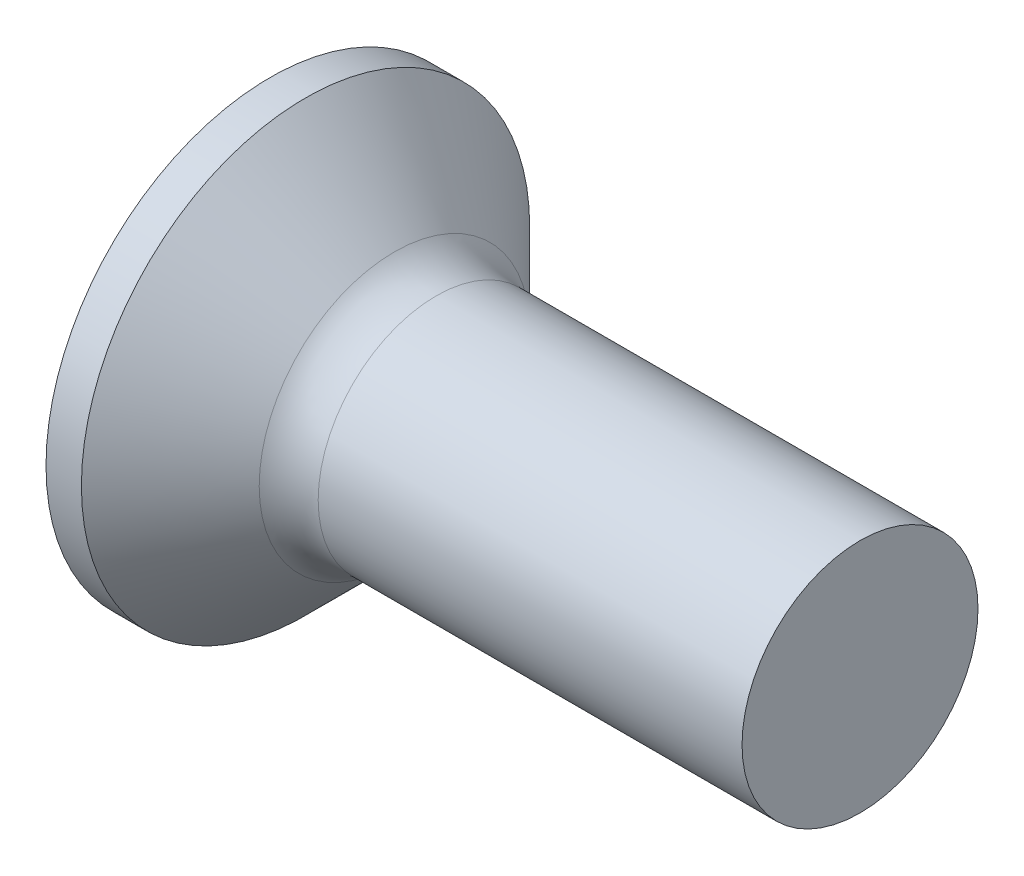
SolidWorks part; units mm, degrees
ref_plane "Plane1" through (0, 0, 0) normal (0, 0, 1) x (1, 0, 0)
ref_plane "Plane2" through (0, 0, 0) normal (0, 1, 0) x (1, 0, 0)
ref_plane "Plane3" through (0, 0, 0) normal (1, 0, 0) x (0, 0, -1)
sketch "BodySke" plane through (0, 0, 0) normal (0, 0, 1) x (1, 0, 0)
  line L0 (0, 0) -> (0, 1.9)
  line L1 (0, 1.9) -> (0.3, 1.9)
  line L2 (1.2, 1) -> (5, 1)
  line L3 (5, 1) -> (5, 0)
  line L4 (5, 0) -> (0, 0)
  line L5 (-6.35, 0) -> (82.55, 0) construction
  line L6 (1.2, -1) -> (5, -1) construction
  line L7 (0.3, -1.9) -> (1.2, -1) construction
  line L8 (0.3, 1.9) -> (1.2, 1)
  line L9 (0, -1.9) -> (0.3, -1.9) construction
  line L10 (1.6, 2.5875) -> (1.6, -6.9375) construction
  line L11 (0, 6.35) -> (0, -3.175) construction
  dimension "Diameter" = 2
  dimension "Length" = 5
  dimension "Head_ht" = 1.2
  dimension "Head_dia" = 3.8
  dimension "Head_ang" = 90
  dimension "D6" = 0.3
  dimension "Advance" = 0.4
  dimension "Thread_nom" = 5
revolve "Base-Revolve" add sketch "BodySke"
cosmetic thread "ThreadCosmetic"
fillet "Fillet1" radius 0.5 1 edges at (1.2, 0, 1)
sketch "Sketch3" plane through (0, 0, 0) normal (-1, 0, 0) x (0, 0, 1)
  line L0 (-0.24, 0.95) -> (0.24, 0.95)
  line L1 (0.24, 0.95) -> (0.24, -0.95)
  line L2 (0.24, -0.95) -> (-0.24, -0.95)
  line L3 (-0.24, -0.95) -> (-0.24, 0.95)
  dimension "D1" = 0.95
  dimension "Cross_dia" = 1.9
  dimension "D2" = 0.24
  dimension "Cross_width" = 0.48
ref_plane "Plane4" through (1.2, 0, 0) normal (-1, 0, 0) x (0, 0, 1)
sketch "Sketch4" plane through (1.2, 0, 0) normal (-1, 0, 0) x (0, 0, 1)
  line L0 (-0.24, 0.3517) -> (0.24, 0.3517)
  line L3 (0.24, 0.3517) -> (0.24, -0.3517)
  line L4 (0.24, -0.3517) -> (-0.24, -0.3517)
  line L5 (-0.24, -0.3517) -> (-0.24, 0.3517)
  dimension "D1" = 0.48
  dimension "D2" = 0.7034
  dimension "D3" = 0.24
  dimension "D4" = 0.3517
loft "Recess" cut profiles "Sketch3", "Sketch4"
pattern_circular "RecPat" count 2 every 90 about axis through (0, 0, 0) along (1, 0, 0) of "Recess"
sketch "RecCorSke" plane through (0, 0, 0) normal (0, 0, 1) x (1, 0, 0)
  line L0 (-3.175, 0) -> (15.875, 0) construction
  line L2 (0, 0) -> (0, 0.4394)
  line L3 (0, 0.4394) -> (1.2, 0.3555)
  line L4 (1.2, 0.3555) -> (1.3155, 0)
  line L5 (1.3155, 0) -> (0, 0)
  dimension "Diameter" = 0.711
  dimension "Depth" = 1.2
  dimension "Draft_angle" = 4
  dimension "Bottom_angle" = 18
revolve "RecessCore" cut sketch "RecCorSke" angle 360 about L0
sketch "ThdSchSke" plane through (0, 0, 0) normal (0, 0, 1) x (1, 0, 0)
  line L0 (1.6, -0.774) -> (1.4418, -1)
  line L1 (1.6, -0.774) -> (1.7582, -1)
  line L2 (1.7582, -1) -> (1.7582, -1.25)
  line L3 (-3.175, 0) -> (5.1513, 0) construction
  line L5 (1.7582, -1.25) -> (1.4418, -1.25)
  line L6 (1.4418, -1.25) -> (1.4418, -1)
  line L7 (0, 1.9) -> (0, -1.9) construction
  dimension "Thread_minor" = 1.548
  dimension "Diameter" = 2
  dimension "Start" = 1.6
  dimension "SideAngle" = 55
  dimension "VeeAngle" = 70
  dimension "Overcut" = 2.5
revolve "ThreadSchematic" [suppressed] cut sketch "ThdSchSke" angle 360 about L3
pattern_linear "ThdSchPat" [suppressed]
equation "\"D1@Sketch3\" = \"Cross_dia@Sketch3\" / 2"
equation "\"D2@Sketch3\" = \"Cross_width@Sketch3\" / 2"
equation "\"Depth@RecCorSke\" = \"Cross_depth@Plane4\""
equation "\"D1@Sketch4\" = \"Cross_width@Sketch3\""
equation "\"D2@Sketch4\" = \"Cross_dia@Sketch3\" - 2.0 * \"Cross_depth@Plane4\" * tan(26.5  * 0.017453292)"
equation "\"D3@Sketch4\" = \"D1@Sketch4\" / 2"
equation "\"D4@Sketch4\" = \"D2@Sketch4\" / 2"
equation "\"Thread_length@ThreadCosmetic\" = ((sgn( (\"Length@BodySke\" - \"Advance@BodySke\" * 1.0 - \"Head_ht@BodySke\" ) - \"Thread_nom@BodySke\" )-1)*( (\"Length@BodySke\" - \"Advance@BodySke\" * 1.0 - \"Head_ht@BodySke\" ) - \"Thread_nom@BodySke\" ))/-2+ \"Thread_nom@BodySke\""
equation "\"Thread_minor@ThdSchSke\" = \"Thread_minor@ThreadCosmetic\""
equation "\"Diameter@ThdSchSke\" = \"Diameter@BodySke\""
equation "\"Overcut@ThdSchSke\" = \"Diameter@BodySke\" * 1.25"
equation "\"Start@ThdSchSke\" = 0.000001 + \"Length@BodySke\" - \"Thread_length@ThreadCosmetic\"  '---Countersunk---"
equation "\"Num_threads@ThdSchPat\" = int( \"Thread_length@ThreadCosmetic\" / \"Advance@BodySke\" + 0.999 )  + 1"
equation "\"Advance@ThdSchPat\" = \"Thread_length@ThreadCosmetic\" /  (\"Num_threads@ThdSchPat\" - 1) 'relax it"
